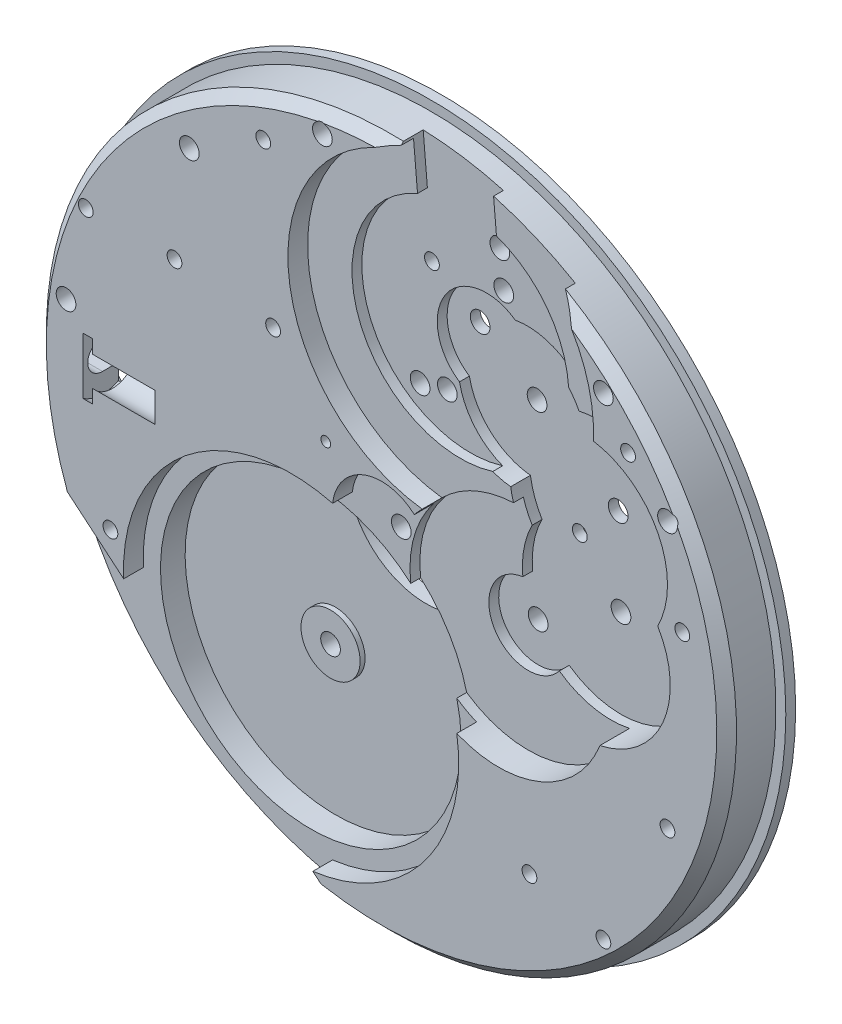
SolidWorks part; units mm, degrees
ref_plane "Alzado" through (0, 0, 0) normal (0, 0, 1) x (1, 0, 0)
ref_plane "Planta" through (0, 0, 0) normal (0, 1, 0) x (1, 0, 0)
ref_plane "Vista lateral" through (0, 0, 0) normal (1, 0, 0) x (0, 0, -1)
sketch "Croquis1" plane through (0, 0, 0) normal (0, 0, 1) x (1, 0, 0)
  circle A0 centre (0, 0) radius 17.5
  dimension "D1" = 35
extrude "Saliente-Extruir1" add sketch "Croquis1" along normal blind 2.5
sketch "Croquis2" plane through (0, 0, 0) normal (0, 0, -1) x (-1, 0, 0)
  circle A0 centre (0, 0) radius 18
  dimension "D1" = 36
extrude "Saliente-Extruir2" add sketch "Croquis2" along normal blind 0.5
chamfer "Chaflán1" distance 0.5 angle 45 1 edges at (17.5, 0, 2.5)
sketch "Croquis4" plane through (0, 0, 2.5) normal (0, 0, 1) x (1, 0, 0)
  line L0 (0, 0) -> (0, -9.0838) construction
  line L1 (0, 0) -> (-4.5875, -7.9458) construction
  circle A0 centre (-4.5875, -7.9458) radius 7.625
  dimension "D1" = 15.25
  dimension "D2" = 9.175
  dimension "D3" = 30
extrude "Cortar-Extruir1" cut sketch "Croquis4" against normal blind 2.25
sketch "Croquis5" plane through (0, 0, 2.5) normal (0, 0, 1) x (1, 0, 0)
  line L0 (-1.6374, -17.9254) -> (-3.4861, -16.3741)
  line L1 (0, 0) -> (-25.7707, 0) construction
  line L2 (-13.0791, -8.3247) -> (-17.3687, -4.7252)
  line L3 (-17.3687, -4.7252) -> (-23, 0) construction
  arc A0 (-3.4861, -16.3741) -> (1.4924, -2.0057) centre (-4.5875, -7.9458) ccw
  circle A1 centre (-4.5875, -7.9458) radius 7.625 construction
  circle A2 centre (0, 0) radius 18 construction
  arc A3 (-17.3687, -4.7252) -> (-1.6374, -17.9254) centre (0, 0) ccw
  arc A4 (1.4924, -2.0057) -> (-2.4832, 0.2896) centre (0, 0) ccw
  arc A5 (-2.4832, 0.2896) -> (-13.0791, -8.3247) centre (-4.5875, -7.9458) ccw
  circle A6 centre (3, 10) radius 7.75
  dimension "D1" = 17
  dimension "D4" = 5
  dimension "D5" = 15.5
  dimension "D2" = 40
  dimension "D3" = 23
  dimension "D6" = 3
  dimension "D7" = 10
extrude "Cortar-Extruir2" cut sketch "Croquis5" against normal blind 1
sketch "Croquis7" plane through (0, 0, 1.5) normal (0, 0, 1) x (1, 0, 0)
  circle A0 centre (0, 0) radius 0.5
  dimension "D1" = 1
extrude "Cortar-Extruir3" cut sketch "Croquis7" against normal through all
sketch "Croquis8" plane through (0, 0, 1.5) normal (0, 0, 1) x (1, 0, 0)
  line L0 (0, 0) -> (3.3821, 0) construction
  line L1 (0, 0) -> (5.9404, -1.5917) construction
  circle A0 centre (5.9404, -1.5917) radius 5.5
  circle A1 centre (3, 10) radius 5.5
  arc A2 (0.9507, 17.4742) -> (8.8251, 15.1119) centre (3, 10) ccw construction
  dimension "D3" = 11
  dimension "D4" = 11
  dimension "D1" = 15
  dimension "D2" = 6.15
sketch "Croquis9" plane through (0, 0, 0.25) normal (0, 0, 1) x (1, 0, 0)
  circle A0 centre (-4.5875, -7.9458) radius 1.5
  circle A1 centre (-4.5875, -7.9458) radius 7.625 construction
  dimension "D1" = 3
extrude "Saliente-Extruir3" add sketch "Croquis9" along normal blind 0.25
sketch "Croquis10" plane through (0, 0, 0.5) normal (0, 0, 1) x (1, 0, 0)
  circle A0 centre (-4.5875, -7.9458) radius 0.5
  circle A1 centre (-4.5875, -7.9458) radius 1.5 construction
  dimension "D1" = 1
extrude "Cortar-Extruir4" cut sketch "Croquis10" against normal through all
extrude "Cortar-Extruir5" cut sketch "Croquis8" against normal blind 0.5 and the other way through all
sketch "Croquis12" plane through (0, 0, 1) normal (0, 0, 1) x (1, 0, 0)
  line L0 (5.9404, -1.5917) -> (10.3846, -1.5917) construction
  line L1 (5.9404, -1.5917) -> (10.1407, 0.8333) construction
  line L2 (3, 10) -> (10, 5.2) construction
  arc A0 (5.6627, 0.3889) -> (7.5168, -2.8226) centre (5.9404, -1.5917) ccw
  arc A1 (6.2436, -1.4167) -> (6.35, -1.5917) centre (10.1407, 0.8333) ccw
  arc A2 (14.0025, 3.1433) -> (9.0146, 9.5908) centre (10, 5.2) ccw
  arc A3 (5.2795, 11.4676) -> (2.4524, 7.3448) centre (3.8247, 9.4345) ccw
  arc A4 (2.4524, 7.3448) -> (5.5491, 4.537) centre (5.8866, 8.0207) ccw
  arc A5 (2.8151, -6.1174) -> (0.4797, -2.2481) centre (5.9404, -1.5917) ccw construction
  circle A6 centre (0, 0) radius 0.5 construction
  arc A7 (7.5168, -2.8226) -> (14.0025, 3.1433) centre (10.1407, 0.8333) ccw
  arc A8 (6.1382, 2.89) -> (5.6627, 0.3889) centre (10.1407, 0.8333) ccw
  circle A9 centre (3, 10) radius 5.5 construction
  arc A10 (5.5491, 4.537) -> (6.1382, 2.89) centre (10, 5.2) ccw
  arc A11 (9.0146, 9.5908) -> (5.2795, 11.4676) centre (5.8866, 8.0207) ccw
  point P5 (3, 10)
  dimension "D1" = 4
  dimension "D4" = 9
  dimension "D5" = 5.2
  dimension "D6" = 10
  dimension "D7" = 9
  dimension "D10" = 5
  dimension "D11" = 7
  dimension "D2" = 4.85
  dimension "D3" = 30
  dimension "D8" = 1
  dimension "D9" = 3.5
extrude "Cortar-Extruir6" cut sketch "Croquis12" against normal blind 0.5 and the other way up to next
sketch "Croquis13" plane through (0, 0, 1.5) normal (0, 0, 1) x (1, 0, 0)
  line L0 (0.5498, 18.1823) -> (1.3342, 9.2166)
  line L1 (4.5346, 18.531) -> (5.1447, 11.5576)
  line L2 (1.3342, 9.2166) -> (5.319, 9.5652) construction
  line L3 (3.3266, 9.3909) -> (8.0496, 9.3909) construction
  line L4 (0.5498, 18.1823) -> (4.5346, 18.531)
  arc A2 (5.2795, 11.4676) -> (2.4524, 7.3448) centre (3.8247, 9.4345) ccw construction
  arc A4 (5.2795, 11.4676) -> (2.4524, 7.3448) centre (3.8247, 9.4345) ccw construction
  arc A5 (5.1447, 11.5576) -> (1.3342, 9.2166) centre (3.8247, 9.4345) ccw
  point P4 (3.3266, 9.3909)
  point P10 (3.3266, 9.3909)
  arc M4 (8.8251, 15.1119) -> (0.9507, 17.4742) centre (0, 0) ccw
  arc M5 (0.9507, 17.4742) -> (2.0611, 2.3071) centre (3, 10) ccw
  arc M9 (4.6399, 4.7502) -> (8.4881, 10.362) centre (3, 10) cw
  dimension "D1" = 4
  dimension "D2" = 95
  dimension "D3" = 9
  dimension "D4" = 7
extrude "Cortar-Extruir7" cut sketch "Croquis13" against normal blind 0.5 and the other way up to surface (1 mm away) contours A5 L1 L0 M9 | L4 L0 L1 M5 M4 | L1 L0 M4 M5 M9 other way up to face at (-7.0319, 2.3778, 2.5)
sketch "Croquis14" plane through (0, 0, 0.5) normal (0, 0, 1) x (1, 0, 0)
  circle A0 centre (3, 10) radius 0.5
  circle A1 centre (5.8866, 8.0207) radius 0.5
  circle A2 centre (10, 5.2) radius 0.5
  circle A3 centre (10.1407, 0.8333) radius 0.5
  circle A4 centre (5.9404, -1.5917) radius 0.5
  arc A5 (6.1382, 2.89) -> (5.6627, 0.3889) centre (10.1407, 0.8333) ccw construction
  arc A6 (14.0025, 3.1433) -> (9.0146, 9.5908) centre (10, 5.2) ccw construction
  arc A7 (2.4524, 7.3448) -> (4.6399, 4.7502) centre (5.8866, 8.0207) ccw construction
  arc A10 (0.8238, 15.0511) -> (4.6399, 4.7502) centre (3, 10) ccw construction
  dimension "D1" = 1
extrude "Cortar-Extruir8" cut sketch "Croquis14" against normal through all
hole_wizard "Diámetro de taladro Ø1.0 (1)1" positions "Croquis16" profile "Croquis15" hole size "Ø1.0" standard "ISO"
sketch "Croquis16" plane through (0, 0, 2.5) normal (0, 0, 1) x (1, 0, 0)
  point P0 (-9.75, 12.25)
  point P1 (-3, 16.25)
  point P3 (-16, 2.5)
  point P5 (11.25, 12)
  point P7 (14.5, 8)
  dimension "D1" = 9.75
  dimension "D2" = 3
  dimension "D3" = 16.25
  dimension "D4" = 12.25
  dimension "D5" = 2.5
  dimension "D6" = 16
  dimension "D7" = 12
  dimension "D8" = 11.25
  dimension "D9" = 8
  dimension "D10" = 14.5
sketch "Croquis15" plane through (-9.75, 12.25, 2.5) normal (1, 0, 0) x (0, -1, 0)
  line L0 (0, 0) -> (0, 1.5504)
  line L1 (0, 1.5504) -> (0.5, 1.25)
  line L2 (0.5, 1.25) -> (0.5, 0)
  line L5 (0.5, 0) -> (0, 0)
  line L10 (0, 1.5504) -> (-0.5, 1.25) construction
  line L11 (0, -6.35) -> (0, 107.95) construction
  dimension "Diámetro de taladro" = 1
  dimension "Profundidad de taladro" = 1.25
  dimension "Ángulo de perforador" = 118
hole_wizard "Taladro roscado M1x0.251" positions "Croquis18" profile "Croquis17" tap size "M1x0.25" standard "KS"
sketch "Croquis18" plane through (0, 0, 2.5) normal (0, 0, 1) x (1, 0, 0)
  circle A0 centre (0, 0) radius 0.5 construction
  point P0 (-13.75, -6.5)
  point P1 (-5.5, 6.5)
  point P3 (-6, 14.5)
  point P5 (-10.5, 7)
  point P7 (7.5, -11)
  point P9 (14.5, -5.5)
  point P20 (12.5, 10)
  point P27 (11.25, -12)
  dimension "D1" = 7.5
  dimension "D2" = 11
  dimension "D3" = 13.75
  dimension "D4" = 6.5
  dimension "D5" = 7
  dimension "D6" = 10.5
  dimension "D7" = 14.5
  dimension "D8" = 5.5
  dimension "D11" = 6.5
  dimension "D12" = 5.5
  dimension "D13" = 6
  dimension "D14" = 14.5
  dimension "D15" = 10
  dimension "D16" = 12.5
  dimension "D19" = 12
  dimension "D20" = 11.25
sketch "Croquis17" plane through (-13.75, -6.5, 2.5) normal (1, 0, 0) x (0, -1, 0)
  line L0 (0, 0) -> (0, 1.7253)
  line L1 (0, 1.7253) -> (0.375, 1.5)
  line L2 (0.375, 1.5) -> (0.375, 0)
  line L5 (0.375, 0) -> (0, 0)
  line L10 (0, 1.7253) -> (-0.375, 1.5) construction
  line L11 (0, -6.35) -> (0, 107.95) construction
  dimension "Diámetro de perforador para roscar" = 0.75
  dimension "Profundidad de perforador para roscar" = 1.5
  dimension "Ángulo de perforador" = 118
cosmetic thread "Rosca de taladro1" parameters "D1"=1.25, "D2"=1
cosmetic thread "Rosca de taladro2" parameters "D1"=1.25, "D2"=1
cosmetic thread "Rosca de taladro3" parameters "D1"=1.25, "D2"=1
cosmetic thread "Rosca de taladro4" parameters "D1"=1.25, "D2"=1
cosmetic thread "Rosca de taladro5" parameters "D1"=1.25, "D2"=1
cosmetic thread "Rosca de taladro6" parameters "D1"=1.25, "D2"=1
cosmetic thread "Rosca de taladro7" parameters "D1"=1.25, "D2"=1
cosmetic thread "Rosca de taladro8" parameters "D1"=1.25, "D2"=1
sketch "Croquis19" plane through (0, 0, 1) normal (0, 0, 1) x (1, 0, 0)
  line L0 (1.8352, 6.6995) -> (3, 10) construction
  line L1 (3, 10) -> (4.4976, 14.2435) construction
  line L2 (5.8866, 8.0207) -> (3, 10) construction
  circle A1 centre (1.8352, 6.6995) radius 0.5
  circle A2 centre (4.4976, 14.2435) radius 0.5
  circle A3 centre (3, 10) radius 0.5 construction
  dimension "D2" = 1
  dimension "D3" = 1
  dimension "D1" = 75
  dimension "D4" = 3.5
  dimension "D5" = 4.5
extrude "Cortar-Extruir9" cut sketch "Croquis19" against normal through all
sketch "Croquis20" plane through (0, 0, -0.5) normal (0, 0, -1) x (-1, 0, 0)
  line L0 (0, 0) -> (2.8284, 2.8284) construction
  line L1 (0, 0) -> (4.8205, 0) construction
  arc A0 (-0.0125, 1.2499) -> (1.2499, -0.0125) centre (0, 0) ccw
  arc A1 (1.2499, -0.0125) -> (-0.0125, 1.2499) centre (2.8284, 2.8284) ccw
  dimension "D1" = 2.5
  dimension "D2" = 6.5
  dimension "D3" = 45
  dimension "D4" = 4
extrude "Cortar-Extruir10" cut sketch "Croquis20" against normal blind 1.25
sketch "Croquis21" plane through (0, 0, -0.5) normal (0, 0, -1) x (-1, 0, 0)
  circle A0 centre (0, 0) radius 4
  dimension "D1" = 8
extrude "Cortar-Extruir11" cut sketch "Croquis21" against normal blind 0.75
sketch "Croquis22" plane through (0, 0, 0.75) normal (0, 0, -1) x (-1, 0, 0)
  circle A0 centre (2.8284, 2.8284) radius 0.25
  dimension "D1" = 0.5
extrude "Cortar-Extruir12" cut sketch "Croquis22" against normal through all
hole_wizard "Taladro roscado M1x0.252" positions "Croquis24" profile "Croquis23" tap size "M1x0.25" standard "KS"
sketch "Croquis24" plane through (0, 0, 2.5) normal (0, 0, 1) x (1, 0, 0)
  point P0 (15.25, 3.5)
  point P1 (-15, 7)
  dimension "D1" = 3.5
  dimension "D2" = 15.25
  dimension "D3" = 15
  dimension "D4" = 7
sketch "Croquis23" plane through (15.25, 3.5, 2.5) normal (1, 0, 0) x (0, -1, 0)
  line L0 (0, 0) -> (0, 1.7253)
  line L1 (0, 1.7253) -> (0.375, 1.5)
  line L2 (0.375, 1.5) -> (0.375, 0)
  line L5 (0.375, 0) -> (0, 0)
  line L10 (0, 1.7253) -> (-0.375, 1.5) construction
  line L11 (0, -6.35) -> (0, 107.95) construction
  dimension "Diámetro de perforador para roscar" = 0.75
  dimension "Profundidad de perforador para roscar" = 1.5
  dimension "Ángulo de perforador" = 118
cosmetic thread "Rosca de taladro9" parameters "D1"=1.25, "D2"=1
cosmetic thread "Rosca de taladro10" parameters "D1"=1.25, "D2"=1
hole_wizard "Diámetro de taladro Ø1.0 (1)2" positions "Croquis27" profile "Croquis26" hole size "Ø1.0" standard "ISO"
sketch "Croquis27" plane through (0, 0, -0.5) normal (0, 0, -1) x (-1, 0, 0)
  line L0 (9.8995, 9.8995) -> (-9.8995, -9.8995) construction
  line L2 (0, 0) -> (7.1735, 0) construction
  point P0 (-9.8995, -9.8995)
  point P1 (9.8995, 9.8995)
  point P8 (0, 0)
  dimension "D1" = 28
  dimension "D2" = 45
sketch "Croquis26" plane through (9.8995, -9.8995, -0.5) normal (1, 0, 0) x (0, 1, 0)
  line L0 (0, 0) -> (0, 2.3004)
  line L1 (0, 2.3004) -> (0.5, 2)
  line L2 (0.5, 2) -> (0.5, 0)
  line L5 (0.5, 0) -> (0, 0)
  line L10 (0, 2.3004) -> (-0.5, 2) construction
  line L11 (0, -6.35) -> (0, 107.95) construction
  dimension "Diámetro de taladro" = 1
  dimension "Profundidad de taladro" = 2
  dimension "Ángulo de perforador" = 118
chamfer "Chaflán2" distance 0.25 angle 45 2 edges at (9.3995, -9.8995, -0.5) (-10.3995, 9.8995, -0.5)
hole_wizard "Taladro roscado M1x0.253" positions "Croquis29" profile "Croquis28" tap size "M1x0.25" standard "KS"
sketch "Croquis29" plane through (0, 0, 1) normal (0, 0, 1) x (1, 0, 0)
  line L0 (3, 10) -> (5.8866, 8.0207) construction
  line L2 (0.4551, 6.2887) -> (3, 10) construction
  line L3 (3, 10) -> (4.6966, 12.4742) construction
  point P0 (0.4551, 6.2887)
  point P1 (4.6966, 12.4742)
  dimension "D1" = 4.5
  dimension "D2" = 3
sketch "Croquis28" plane through (0.4551, 6.2887, 1) normal (1, 0, 0) x (0, -1, 0)
  line L0 (0, 0) -> (0, 1.4753)
  line L1 (0, 1.4753) -> (0.375, 1.25)
  line L2 (0.375, 1.25) -> (0.375, 1)
  line L3 (0.375, 1) -> (0.5, 1)
  line L4 (0.5, 1) -> (0.5, 0)
  line L5 (0.5, 0) -> (0, 0)
  line L10 (0, 1.4753) -> (-0.375, 1.25) construction
  line L11 (0, -6.35) -> (0, 107.95) construction
  dimension "Diámetro de perforador para roscar" = 0.75
  dimension "Profundidad de perforador para roscar" = 1.25
  dimension "Diámetro mayor de rosca" = 1
  dimension "Profundidad de rosca" = 1
  dimension "Ángulo de perforador" = 118
ref_plane "Plano1" through (-17.5, 0, 0) normal (-1, 0, 0) x (0, 0, 1)
sketch "Croquis30" plane through (-17.5, 0, 0) normal (-1, 0, 0) x (0, 0, 1)
  line L0 (-0.5, 18) -> (-0.5, -18) construction
  circle A0 centre (1.5, 0) radius 0.75
  dimension "D2" = 1.5
  dimension "D1" = 2
extrude "Cortar-Extruir13" cut sketch "Croquis30" against normal blind 2.35
sketch "Croquis31" plane through (-15.15, 0, 0) normal (-1, 0, 0) x (0, 0, 1)
  circle A0 centre (1.5, 0) radius 1.75
  dimension "D1" = 3.5
extrude "Cortar-Extruir14" cut sketch "Croquis31" against normal blind 0.5
sketch "Croquis32" plane through (0, 0, -0.5) normal (0, 0, -1) x (-1, 0, 0)
  line L0 (8.6082, 6.1801) -> (8.785, 6.3569)
  line L1 (8.6082, 6.1801) -> (9.3621, 6.1801) construction
  arc A0 (8.6082, 6.1801) -> (7.8626, -0.6617) centre (7.6, 2.8284) ccw
  arc A1 (10.9015, 8.3463) -> (8.785, 6.3569) centre (10.1, 7.0784) ccw
  arc A4 (17.1934, 0.6702) -> (16.7694, 2.8787) centre (14.25, 1.25) ccw
  arc A5 (7.8626, -0.6617) -> (9.7857, -1.9997) centre (9.75, 0) ccw
  arc A6 (9.7857, -1.9997) -> (17.1934, 0.6702) centre (13.25, 0) ccw
  arc A11 (16.7694, 2.8787) -> (10.9015, 8.3463) centre (12.1, 3.75) ccw
  dimension "D3" = 4.25
  dimension "D4" = 2.5
  dimension "D5" = 0.25
  dimension "D8" = 4.75
  dimension "D9" = 6
  dimension "D14" = 8
  dimension "D17" = 4.5
  dimension "D25" = 3.5
  dimension "D10" = 2
  dimension "D11" = 3
  dimension "D6" = 7.6
  dimension "D7" = 9.75
  dimension "D12" = 3.5
  dimension "D13" = 1.25
  dimension "D15" = 4.5
  dimension "D16" = 3.75
  dimension "D20" = 135
extrude "Cortar-Extruir15" cut sketch "Croquis32" against normal blind 1.2
sketch "Croquis33" plane through (-14.65, 0, 0) normal (-1, 0, 0) x (0, 0, 1)
  circle A0 centre (1.5, 0) radius 1.25
  arc A1 (2.5, 1.4361) -> (0.7, 1.5564) centre (1.5, 0) ccw construction
  dimension "D1" = 2.5
extrude "Cortar-Extruir16" cut sketch "Croquis33" against normal blind 3.15
hole_wizard "Diámetro de taladro Ø0.2 (0.2)1" positions "Croquis37" profile "Croquis36" hole size "Ø0.2" standard "ISO"
sketch "Croquis37" plane through (-11.5, 0, 0) normal (-1, 0, 0) x (0, 0, 1)
  arc A0 (0.7, -0.9605) -> (2.5, -0.75) centre (1.5, 0) ccw construction
  point P0 (1.5, 0)
sketch "Croquis36" plane through (-11.5, 0, 1.5) normal (0, 1, 0) x (0, 0, 1)
  line L0 (0, 0) -> (0, 2.0601)
  line L1 (0, 2.0601) -> (0.1, 2)
  line L2 (0.1, 2) -> (0.1, 0)
  line L5 (0.1, 0) -> (0, 0)
  line L10 (0, 2.0601) -> (-0.1, 2) construction
  line L11 (0, -6.35) -> (0, 107.95) construction
  dimension "Diámetro de taladro" = 0.2
  dimension "Profundidad de taladro" = 2
  dimension "Ángulo de perforador" = 118
sketch "Croquis38" plane through (0, 0, 0.7) normal (0, 0, -1) x (-1, 0, 0)
  circle A0 centre (7.6, 2.8284) radius 0.75
  circle A1 centre (9.75, 0) radius 0.75
  arc A2 (5.0374, 0.4445) -> (7.8626, -0.6617) centre (7.6, 2.8284) ccw construction
  arc A3 (7.8626, -0.6617) -> (8.1552, -1.2069) centre (9.75, 0) ccw construction
  dimension "D1" = 1.5
  dimension "D2" = 1.5
extrude "Saliente-Extruir4" add sketch "Croquis38" along normal blind 0.2
sketch "Croquis41" plane through (0, 0, 0.7) normal (0, 0, -1) x (-1, 0, 0)
  line L0 (15.15, 1.5564) -> (15.15, -1.5564) construction
  line L1 (15.15, 0.75) -> (17.1791, 0.75)
  line L2 (15.15, 0.75) -> (15.15, -0.75)
  line L3 (15.15, -0.75) -> (17.1791, -0.75)
  arc A0 (9.7857, -1.9997) -> (17.1934, 0.6702) centre (13.25, 0) ccw construction
  arc A1 (17.1791, -0.75) -> (17.1791, 0.75) centre (13.25, 0) ccw
  point P4 (15.15, 0)
  dimension "D1" = 1.5
extrude "Cortar-Extruir17" cut sketch "Croquis41" against normal up to next
sketch "Croquis42" plane through (0, 0, 0.7) normal (0, 0, -1) x (-1, 0, 0)
  circle A0 centre (13.3284, -2.1716) radius 0.5608
  dimension "D1" = 5
  dimension "D2" = 10.5
extrude "Saliente-Extruir5" add sketch "Croquis42" along normal blind 0.2
hole_wizard "Taladro roscado M1x0.255" positions "Croquis44" profile "Croquis43" tap size "M1x0.25" standard "KS"
sketch "Croquis44" plane through (0, 0, 0.5) normal (0, 0, -1) x (-1, 0, 0)
  circle A0 centre (13.3284, -2.1716) radius 0.5608 construction
  arc A1 (5.0374, 0.4445) -> (7.8626, -0.6617) centre (7.6, 2.8284) ccw construction
  point P0 (13.3284, -2.1716)
  point P1 (7.6, 2.8284)
sketch "Croquis43" plane through (-13.3284, -2.1716, 0.5) normal (1, 0, 0) x (0, 1, 0)
  line L0 (0, 0) -> (0, 1.2253)
  line L1 (0, 1.2253) -> (0.375, 1)
  line L2 (0.375, 1) -> (0.375, 0)
  line L5 (0.375, 0) -> (0, 0)
  line L10 (0, 1.2253) -> (-0.375, 1) construction
  line L11 (0, -6.35) -> (0, 107.95) construction
  dimension "Diámetro de perforador para roscar" = 0.75
  dimension "Profundidad de perforador para roscar" = 1
  dimension "Ángulo de perforador" = 118
cosmetic thread "Rosca de taladro12" parameters "D1"=0.75, "D2"=1
cosmetic thread "Rosca de taladro13" parameters "D1"=0.75, "D2"=1
hole_wizard "Diámetro de taladro Ø0.5 (0.5)1" positions "Croquis46" profile "Croquis45" hole size "Ø0.5" standard "ISO"
sketch "Croquis46" plane through (0, 0, 0.7) normal (0, 0, -1) x (-1, 0, 0)
  line L1 (15.15, 1.5564) -> (15.15, 0.75) construction
  line L2 (14.65, 1.5564) -> (15.15, 1.5564) construction
  point P0 (15.4, 3.0564)
  dimension "D1" = 0.25
  dimension "D2" = 1.5
sketch "Croquis45" plane through (-15.4, 3.0564, 0.7) normal (1, 0, 0) x (0, 1, 0)
  line L0 (0, 0) -> (0, 1.1502)
  line L1 (0, 1.1502) -> (0.25, 1)
  line L2 (0.25, 1) -> (0.25, 0)
  line L5 (0.25, 0) -> (0, 0)
  line L10 (0, 1.1502) -> (-0.25, 1) construction
  line L11 (0, -6.35) -> (0, 107.95) construction
  dimension "Diámetro de taladro" = 0.5
  dimension "Profundidad de taladro" = 1
  dimension "Ángulo de perforador" = 118
sketch "Croquis47" plane through (0, 0, 0.7) normal (0, 0, -1) x (-1, 0, 0)
  circle A0 centre (12.35, 7.5) radius 0.25
  arc A2 (10.9015, 8.3463) -> (8.785, 6.3569) centre (10.1, 7.0784) ccw construction
  arc A3 (16.7694, 2.8787) -> (10.9015, 8.3463) centre (12.1, 3.75) ccw construction
  circle A4 centre (10.1, 7.0784) radius 0.75
  dimension "D1" = 0.5
  dimension "D2" = 2.25
  dimension "D3" = 3.75
  dimension "D4" = 1.5
extrude "Saliente-Extruir6" add sketch "Croquis47" along normal blind 0.5
sketch "Croquis48" plane through (0, 0, -0.5) normal (0, 0, -1) x (-1, 0, 0)
  circle A0 centre (-9, 4.2) radius 2.5
  circle A1 centre (-2, 11) radius 2.5
  circle A3 centre (-3, 10) radius 0.5 construction
  circle A4 centre (-10, 5.2) radius 0.5 construction
  dimension "D1" = 5
  dimension "D2" = 5
  dimension "D3" = 1
  dimension "D4" = 1
  dimension "D5" = 1
  dimension "D6" = 1
extrude "Cortar-Extruir18" cut sketch "Croquis48" against normal blind 0.5
hole_wizard "Taladro roscado M1x0.256" positions "Croquis50" profile "Croquis49" tap size "M1x0.25" standard "KS" end condition through all
sketch "Croquis50" plane through (0, 0, 0) normal (0, 0, -1) x (-1, 0, 0)
  line L4 (-10, 5.2) -> (-8.0555, 3.2555) construction
  line L6 (-9.0277, 4.2277) -> (-8.1716, 4.2277) construction
  line L10 (-3, 10) -> (-1.0555, 11.9445) construction
  line L12 (-2.0277, 10.9723) -> (-1.5482, 10.9723) construction
  circle A1 centre (-10, 5.2) radius 0.5 construction
  circle A3 centre (-3, 10) radius 0.5 construction
  point P0 (-8.0555, 3.2555)
  point P1 (-1.0555, 11.9445)
  point P21 (-9.0277, 4.2277)
  point P40 (-2.0277, 10.9723)
  dimension "D1" = 2.75
  dimension "D2" = 45
  dimension "D3" = 2.75
  dimension "D4" = 45
sketch "Croquis49" plane through (8.0555, 3.2555, 0) normal (1, 0, 0) x (0, 1, 0)
  line L0 (0, 0) -> (0, 2.5249)
  line L1 (0, 2.5249) -> (0.375, 2.5249)
  line L2 (0.375, 2.5249) -> (0.375, 0)
  line L5 (0.375, 0) -> (0, 0)
  line L11 (0, -6.35) -> (0, 107.95) construction
  dimension "Diámetro de perforador para roscar hasta el siguiente" = 0.75
  dimension "Profundidad de perforador para roscar hasta el siguiente" = 2.5249
cosmetic thread "Rosca de taladro14" parameters "D2"=1
cosmetic thread "Rosca de taladro15" parameters "D2"=1
